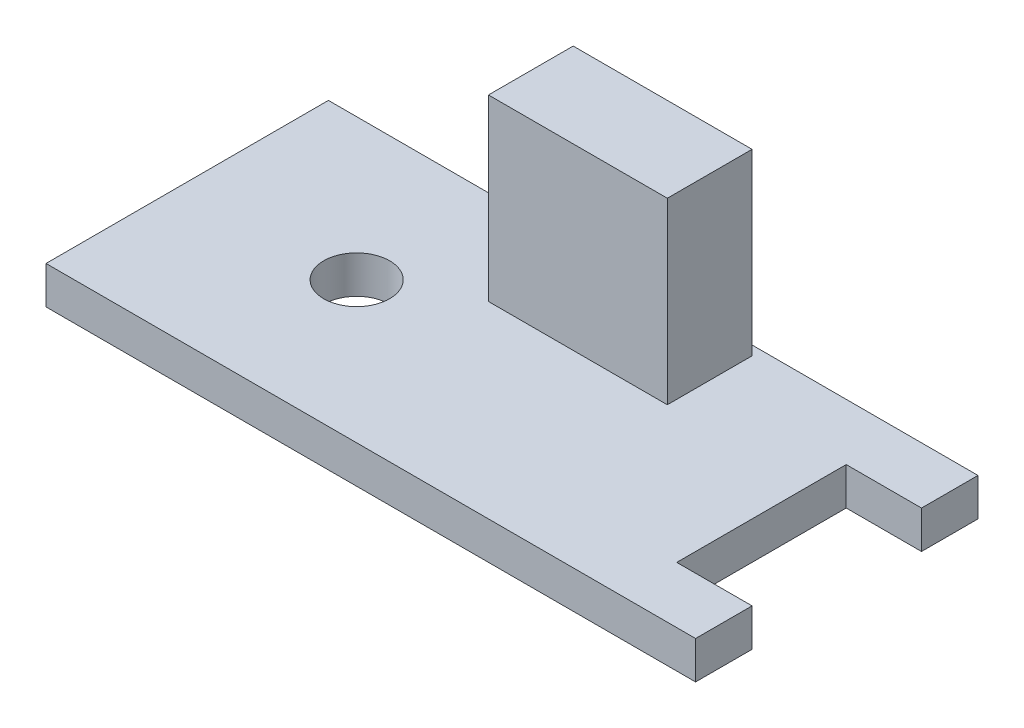
SolidWorks part; units mm, degrees
ref_plane "Front Plane" through (0, 0, 0) normal (0, 0, 1) x (1, 0, 0)
ref_plane "Top Plane" through (0, 0, 0) normal (0, 1, 0) x (1, 0, 0)
ref_plane "Right Plane" through (0, 0, 0) normal (1, 0, 0) x (0, 0, -1)
sketch "Sketch1" plane through (0, 0, 0) normal (0, 1, 0) x (1, 0, 0)
  line L0 (17.25, 4.5) -> (13.25, 4.5)
  line L1 (-17.25, -7.5) -> (17.25, -7.5)
  line L2 (-17.25, -7.5) -> (-17.25, 7.5)
  line L3 (-17.25, 7.5) -> (17.25, 7.5)
  line L4 (17.25, -7.5) -> (17.25, -4.5)
  line L5 (-17.25, -7.5) -> (17.25, 7.5) construction
  line L6 (-17.25, 7.5) -> (17.25, -7.5) construction
  line L7 (13.25, 4.5) -> (13.25, -4.5)
  line L8 (13.25, -4.5) -> (17.25, -4.5)
  line L9 (17.25, 4.5) -> (17.25, 7.5)
  circle A0 centre (-8.25, 0) radius 1.75
  point P0 (0, 0)
  dimension "D6" = 3.5
  dimension "D1" = 34.5
  dimension "D2" = 15
  dimension "D3" = 3
  dimension "D4" = 3
  dimension "D5" = 4
  dimension "D7" = 9
extrude "Boss-Extrude1" add sketch "Sketch1" along normal blind 2
sketch "Sketch2" plane through (0, 2, 0) normal (0, 1, 0) x (1, 0, 0)
  line L0 (-17.25, 7.5) -> (-17.25, -7.5) construction
  line L1 (-3.75, 7) -> (5.75, 7)
  line L2 (-3.75, 7) -> (-3.75, 2.5)
  line L3 (-3.75, 2.5) -> (5.75, 2.5)
  line L4 (5.75, 7) -> (5.75, 2.5)
  line L5 (-3.75, 7) -> (5.75, 2.5) construction
  line L6 (-3.75, 2.5) -> (5.75, 7) construction
  line L9 (17.25, 7.5) -> (-17.25, 7.5) construction
  point P0 (1, 4.75)
  dimension "D1" = 9.5
  dimension "D2" = 4.5
  dimension "D3" = 23
  dimension "D4" = 0.5
extrude "Boss-Extrude2" add sketch "Sketch2" along normal blind 9.5
